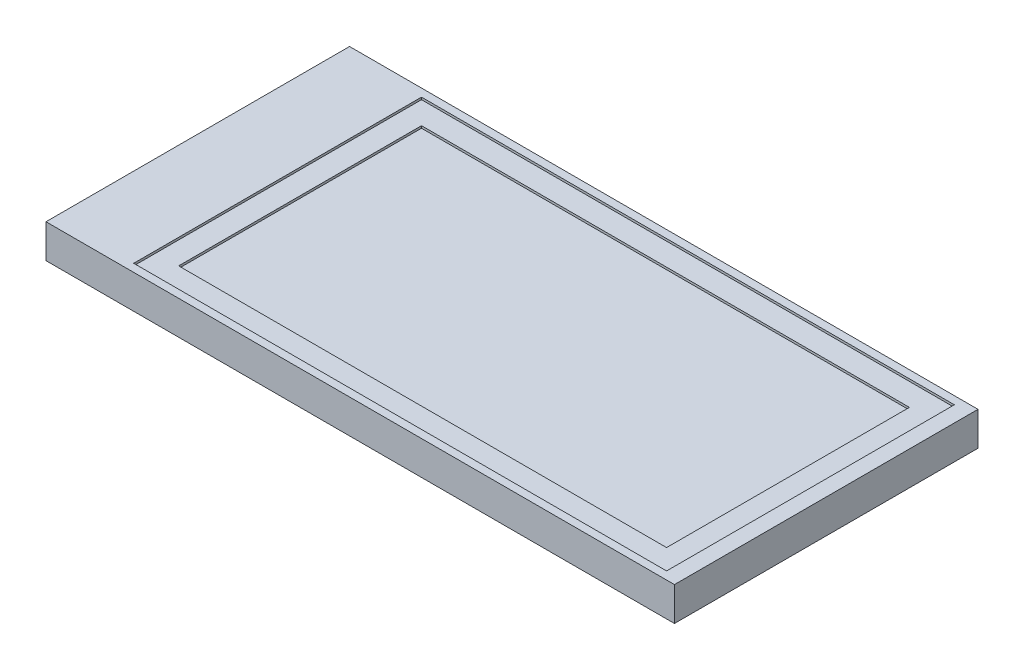
SolidWorks part; units mm, degrees
ref_plane "Спереди" through (0, 0, 0) normal (0, 0, 1) x (1, 0, 0)
ref_plane "Сверху" through (0, 0, 0) normal (0, 1, 0) x (1, 0, 0)
ref_plane "Справа" through (0, 0, 0) normal (1, 0, 0) x (0, 0, -1)
other "Configuration Table"
sketch "Sketch1" plane through (0, 0, 0) normal (0, 1, 0) x (1, 0, 0)
  line L9 (12.55, -6.75) -> (-15.4, -6.75)
  line L10 (12.55, -6.75) -> (12.55, 6.75)
  line L11 (12.55, 6.75) -> (-15.4, 6.75)
  line L12 (-15.4, -6.75) -> (-15.4, 6.75)
extrude "Boss-Extrude1" add sketch "Sketch1" along normal blind 1.5
sketch "Sketch2" plane through (0, 1.5, 0) normal (0, 1, 0) x (1, 0, 0)
  line L0 (-10.85, -5.4) -> (10.85, -5.4)
  line L1 (-10.85, -5.4) -> (-10.85, 5.4)
  line L2 (-10.85, 5.4) -> (10.85, 5.4)
  line L3 (10.85, -5.4) -> (10.85, 5.4)
  point P0 (0, 0)
extrude "Cut-Extrude1" cut sketch "Sketch2" against normal blind 0.2
sketch "Sketch3" plane through (0, 1.5, 0) normal (0, 1, 0) x (1, 0, 0)
  line L1 (-11.85, -6.4) -> (11.85, -6.4)
  line L2 (-11.85, -6.4) -> (-11.85, 6.4)
  line L3 (-11.85, 6.4) -> (11.85, 6.4)
  line L4 (11.85, -6.4) -> (11.85, 6.4)
  line L5 (-11.85, -6.4) -> (11.85, 6.4) construction
  line L6 (-11.85, 6.4) -> (11.85, -6.4) construction
  point P0 (0, 0)
extrude "Cut-Extrude2" cut sketch "Sketch3" against normal blind 0.1
